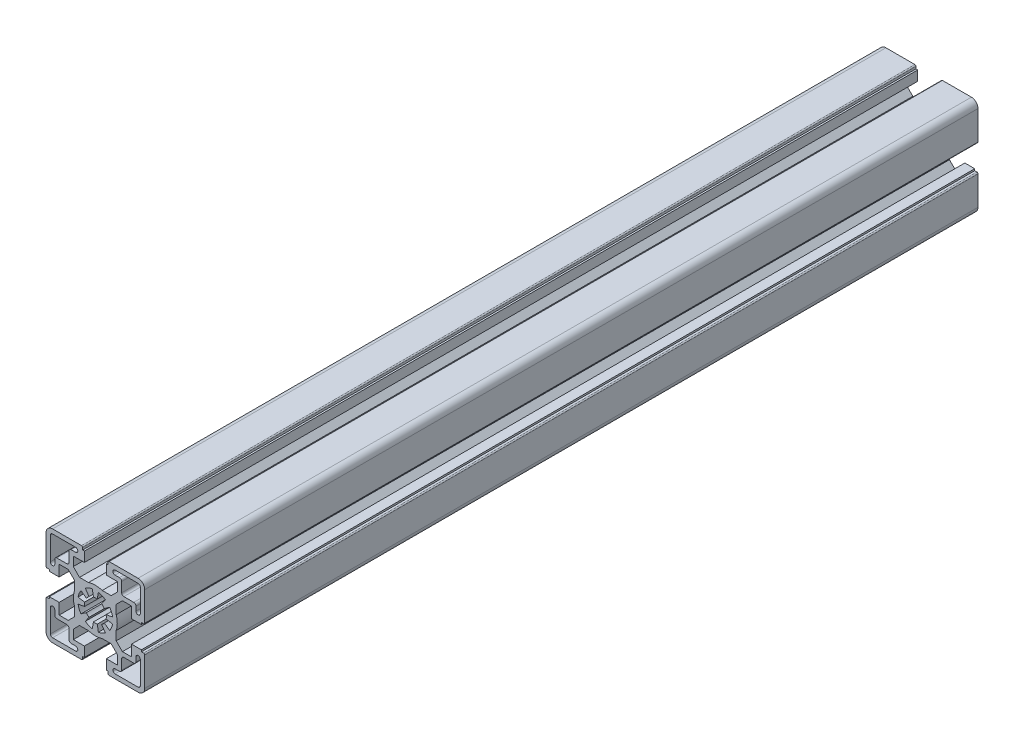
SolidWorks part; units mm, degrees
material "7079 Alloy"
ref_plane "Front Plane" through (0, 0, 0) normal (0, 0, 1) x (1, 0, 0)
ref_plane "Top Plane" through (0, 0, 0) normal (0, 1, 0) x (1, 0, 0)
ref_plane "Right Plane" through (0, 0, 0) normal (1, 0, 0) x (0, 0, -1)
sketch "Sketch1" plane through (0, 0, 0) normal (0, 0, 1) x (1, 0, 0)
  line L0 (0, 34.901) -> (0, -38.8683) construction
  line L1 (-27.7848, 0) -> (42.6814, 0) construction
  line L88 (0.8682, 4.924) -> (1.3892, 7.8784)
  line L89 (-0.8682, 4.924) -> (-1.3892, 7.8785)
  line L90 (-4.5886, 6.5532) -> (-2.8679, 4.0957)
  line L91 (-4.0957, 2.8679) -> (-6.5532, 4.5886)
  line L92 (-7.8784, 1.3892) -> (-4.924, 0.8682)
  line L93 (-7.8785, -1.3892) -> (-4.924, -0.8682)
  line L94 (-6.5532, -4.5886) -> (-4.0957, -2.8679)
  line L95 (-4.5886, -6.5532) -> (-2.8679, -4.0957)
  line L96 (-1.3892, -7.8784) -> (-0.8682, -4.924)
  line L97 (0.8682, -4.924) -> (1.3892, -7.8784)
  line L98 (4.5886, -6.5532) -> (2.8679, -4.0957)
  line L99 (4.0957, -2.8679) -> (6.5532, -4.5886)
  line L100 (7.8784, -1.3892) -> (4.924, -0.8682)
  line L101 (4.924, 0.8682) -> (7.8784, 1.3892)
  line L102 (4.0957, 2.8679) -> (6.5532, 4.5886)
  line L103 (2.8679, 4.0957) -> (4.5886, 6.5532)
  line L104 (-5, -16.4999) -> (-5, -20.9999)
  line L105 (-5, -20.9999) -> (-5.8, -20.9999)
  line L106 (-5.8, -20.9999) -> (-5.8, -22)
  line L107 (-6.3, -22.5) -> (-19.5, -22.5)
  line L108 (-22.5, -19.5) -> (-22.5, -6.2999)
  line L109 (-22, -5.7999) -> (-21, -5.7999)
  line L110 (-21, -5.7999) -> (-21, -4.9999)
  line L111 (-21, -4.9999) -> (-16.5, -4.9999)
  line L112 (-16.5, -4.9999) -> (-16.5, -10.0499)
  line L113 (-16.5, -10.0499) -> (-12.3429, -10.0499)
  line L114 (-12.3429, -10.0499) -> (-9.5, -7.207)
  line L115 (-9.5, -7.207) -> (-9.5, -3.1226)
  line L116 (-9.5, 3.1227) -> (-9.5, 7.207)
  line L117 (-9.5, 7.207) -> (-12.3429, 10.0499)
  line L118 (-12.3429, 10.0499) -> (-16.5, 10.0499)
  line L119 (-16.5, 10.0499) -> (-16.5, 4.9999)
  line L120 (-16.5, 4.9999) -> (-21, 4.9999)
  line L121 (-21, 4.9999) -> (-21, 5.7999)
  line L122 (-21, 5.7999) -> (-22, 5.7999)
  line L123 (-22.5, 6.2999) -> (-22.5, 19.5)
  line L124 (-19.5, 22.5) -> (-6.3, 22.5)
  line L125 (-5.7999, 21.9999) -> (-5.7999, 20.9999)
  line L126 (-5.7999, 20.9999) -> (-5, 20.9999)
  line L127 (-5, 20.9999) -> (-5, 16.5)
  line L128 (-5, 16.5) -> (-10.0501, 16.5)
  line L129 (-10.0501, 16.5) -> (-10.0501, 12.3428)
  line L130 (-10.0501, 12.3428) -> (-7.2072, 9.4999)
  line L131 (-7.2072, 9.4999) -> (-3.1228, 9.4999)
  line L132 (3.1226, 9.4999) -> (7.207, 9.4999)
  line L133 (7.207, 9.4999) -> (10.0499, 12.3428)
  line L134 (10.0499, 12.3428) -> (10.0499, 16.5)
  line L135 (10.0499, 16.5) -> (5, 16.5)
  line L136 (5, 16.5) -> (5, 21)
  line L137 (5, 21) -> (5.7999, 21)
  line L138 (5.7999, 21) -> (5.7999, 21.9999)
  line L139 (6.3, 22.5) -> (19.5001, 22.5)
  line L140 (22.5001, 6.2999) -> (22.5001, 19.5)
  line L141 (22.0001, 5.7999) -> (21, 5.7999)
  line L142 (21, 5.7999) -> (21, 4.9999)
  line L143 (21, 4.9999) -> (16.5, 4.9999)
  line L144 (16.5, 4.9999) -> (16.5, 10.0499)
  line L145 (16.5, 10.0499) -> (12.3429, 10.0499)
  line L146 (12.3429, 10.0499) -> (9.4999, 7.207)
  line L147 (9.4999, 7.207) -> (9.4999, 3.1227)
  line L148 (9.4999, -3.1226) -> (9.4999, -7.207)
  line L149 (9.4999, -7.207) -> (12.3429, -10.0499)
  line L150 (12.3429, -10.0499) -> (16.5, -10.0499)
  line L151 (16.5, -10.0499) -> (16.5, -4.9999)
  line L152 (16.5, -4.9999) -> (21, -4.9999)
  line L153 (21, -4.9999) -> (21, -5.7999)
  line L154 (21, -5.7999) -> (22.0001, -5.7999)
  line L155 (22.5001, -6.2999) -> (22.5001, -19.5)
  line L156 (6.3, -22.5) -> (19.5001, -22.5)
  line L157 (5.8, -22) -> (5.8, -20.9999)
  line L158 (5.8, -20.9999) -> (5, -20.9999)
  line L159 (5, -20.9999) -> (5, -16.4999)
  line L160 (5, -16.4999) -> (10.0499, -16.4999)
  line L161 (10.0499, -16.4999) -> (10.0499, -12.3428)
  line L162 (10.0499, -12.3428) -> (7.2069, -9.4998)
  line L163 (7.2069, -9.4998) -> (3.1226, -9.4998)
  line L164 (-3.1228, -9.4998) -> (-7.2071, -9.4998)
  line L165 (-7.2071, -9.4998) -> (-10.0501, -12.3428)
  line L166 (-10.0501, -12.3428) -> (-10.0501, -16.4999)
  line L167 (-10.0501, -16.4999) -> (-5, -16.4999)
  line L168 (-17.5001, -12) -> (-13.0001, -12)
  line L169 (-12.0001, -17.4999) -> (-12.0001, -13)
  line L170 (-11.0001, -18.4999) -> (-9.0001, -18.4999)
  line L171 (-19.5001, -20.5) -> (-9.0001, -20.5)
  line L172 (-20.5001, -19.5) -> (-20.5001, -8.9999)
  line L173 (-18.5001, -11) -> (-18.5001, -8.9999)
  line L174 (13, -12) -> (17.5, -12)
  line L175 (12, -17.4999) -> (12, -13)
  line L176 (9, -18.4999) -> (11, -18.4999)
  line L177 (9, -20.5) -> (19.5, -20.5)
  line L178 (20.5, -19.5) -> (20.5, -9.0001)
  line L179 (18.5, -11) -> (18.5, -9.0001)
  line L180 (-17.5001, 12) -> (-13.0001, 12)
  line L181 (-12.0001, 13) -> (-12.0001, 17.4999)
  line L182 (-11.0001, 18.4999) -> (-9.0001, 18.4999)
  line L183 (-19.5001, 20.5) -> (-9.0001, 20.5)
  line L184 (-20.5001, 8.9999) -> (-20.5001, 19.5)
  line L185 (-18.5001, 8.9999) -> (-18.5001, 11)
  line L186 (13, 12) -> (17.5, 12)
  line L187 (12, 13) -> (12, 17.4999)
  line L188 (9, 18.4999) -> (11, 18.4999)
  line L189 (9, 20.5) -> (19.5, 20.5)
  line L190 (20.5, 9.0001) -> (20.5, 19.5)
  line L191 (18.5, 9.0001) -> (18.5, 11)
  arc A56 (0.8682, 4.924) -> (-0.8682, 4.924) centre (0, 0) ccw
  arc A57 (-1.3892, 7.8785) -> (-4.5886, 6.5532) centre (0, 0) ccw
  arc A58 (-2.8679, 4.0957) -> (-4.0957, 2.8679) centre (0, 0) ccw
  arc A59 (-6.5532, 4.5886) -> (-7.8784, 1.3892) centre (0, 0) ccw
  arc A60 (-4.924, 0.8682) -> (-4.924, -0.8682) centre (0, 0) ccw
  arc A61 (-7.8785, -1.3892) -> (-6.5532, -4.5886) centre (0, 0) ccw
  arc A62 (-4.0957, -2.8679) -> (-2.8679, -4.0957) centre (0, 0) ccw
  arc A63 (-4.5886, -6.5532) -> (-1.3892, -7.8784) centre (0, 0) ccw
  arc A64 (-0.8682, -4.924) -> (0.8682, -4.924) centre (0, 0) ccw
  arc A65 (1.3892, -7.8784) -> (4.5886, -6.5532) centre (0, 0) ccw
  arc A66 (2.8679, -4.0957) -> (4.0957, -2.8679) centre (0, 0) ccw
  arc A67 (6.5532, -4.5886) -> (7.8784, -1.3892) centre (0, 0) ccw
  arc A68 (4.924, -0.8682) -> (4.924, 0.8682) centre (0, 0) ccw
  arc A69 (7.8784, 1.3892) -> (6.5532, 4.5886) centre (0, 0) ccw
  arc A70 (4.0957, 2.8679) -> (2.8679, 4.0957) centre (0, 0) ccw
  arc A71 (4.5886, 6.5532) -> (1.3892, 7.8784) centre (0, 0) ccw
  arc A72 (-6.3, -22.5) -> (-5.8, -22) centre (-6.3, -22) ccw
  arc A73 (-22.5, -19.5) -> (-19.5, -22.5) centre (-19.5, -19.5) ccw
  arc A74 (-22, -5.7999) -> (-22.5, -6.2999) centre (-22, -6.2999) ccw
  arc A75 (-9.5, 3.1227) -> (-9.5, -3.1226) centre (0, 0.0001) ccw
  arc A76 (-22.5, 6.2999) -> (-22, 5.7999) centre (-22, 6.2999) ccw
  arc A77 (-19.5, 22.5) -> (-22.5, 19.5) centre (-19.5, 19.5) ccw
  arc A78 (-5.7999, 21.9999) -> (-6.3, 22.5) centre (-6.3, 21.9999) ccw
  arc A79 (3.1226, 9.4999) -> (-3.1228, 9.4999) centre (-0.0001, -0.0001) ccw
  arc A80 (6.3, 22.5) -> (5.7999, 21.9999) centre (6.3, 21.9999) ccw
  arc A81 (22.5001, 19.5) -> (19.5001, 22.5) centre (19.5001, 19.5) ccw
  arc A82 (22.0001, 5.7999) -> (22.5001, 6.2999) centre (22.0001, 6.2999) ccw
  arc A83 (9.4999, -3.1226) -> (9.4999, 3.1227) centre (0, 0.0001) ccw
  arc A84 (22.5001, -6.2999) -> (22.0001, -5.7999) centre (22.0001, -6.2999) ccw
  arc A85 (19.5001, -22.5) -> (22.5001, -19.5) centre (19.5001, -19.5) ccw
  arc A86 (5.8, -22) -> (6.3, -22.5) centre (6.3, -22) ccw
  arc A87 (-3.1228, -9.4998) -> (3.1226, -9.4998) centre (-0.0001, 0.0001) ccw
  arc A88 (-18.5001, -11) -> (-17.5001, -12) centre (-17.5001, -11) ccw
  arc A89 (-12.0001, -13) -> (-13.0001, -12) centre (-13.0001, -13) ccw
  arc A90 (-12.0001, -17.4999) -> (-11.0001, -18.4999) centre (-11.0001, -17.4999) ccw
  arc A91 (-9.0001, -20.5) -> (-9.0001, -18.4999) centre (-9.0001, -19.5) ccw
  arc A92 (-20.5001, -19.5) -> (-19.5001, -20.5) centre (-19.5001, -19.5) ccw
  arc A93 (-18.5001, -8.9999) -> (-20.5001, -8.9999) centre (-19.5001, -8.9999) ccw
  arc A94 (17.5, -12) -> (18.5, -11) centre (17.5, -11) ccw
  arc A95 (13, -12) -> (12, -13) centre (13, -13) ccw
  arc A96 (11, -18.4999) -> (12, -17.4999) centre (11, -17.4999) ccw
  arc A97 (9, -18.4999) -> (9, -20.5) centre (9, -19.5) ccw
  arc A98 (19.5, -20.5) -> (20.5, -19.5) centre (19.5, -19.5) ccw
  arc A99 (20.5, -9.0001) -> (18.5, -9.0001) centre (19.5, -9.0001) ccw
  arc A100 (-17.5001, 12) -> (-18.5001, 11) centre (-17.5001, 11) ccw
  arc A101 (-13.0001, 12) -> (-12.0001, 13) centre (-13.0001, 13) ccw
  arc A102 (-11.0001, 18.4999) -> (-12.0001, 17.4999) centre (-11.0001, 17.4999) ccw
  arc A103 (-9.0001, 18.4999) -> (-9.0001, 20.5) centre (-9.0001, 19.5) ccw
  arc A104 (-19.5001, 20.5) -> (-20.5001, 19.5) centre (-19.5001, 19.5) ccw
  arc A105 (-20.5001, 8.9999) -> (-18.5001, 8.9999) centre (-19.5001, 8.9999) ccw
  arc A106 (18.5, 11) -> (17.5, 12) centre (17.5, 11) ccw
  arc A107 (12, 13) -> (13, 12) centre (13, 13) ccw
  arc A108 (12, 17.4999) -> (11, 18.4999) centre (11, 17.4999) ccw
  arc A109 (9, 20.5) -> (9, 18.4999) centre (9, 19.5) ccw
  arc A110 (20.5, 19.5) -> (19.5, 20.5) centre (19.5, 19.5) ccw
  arc A111 (18.5, 9.0001) -> (20.5, 9.0001) centre (19.5, 9.0001) ccw
  dimension "D5" = 10
  dimension "D1" = 45.0001
  dimension "D2" = 44.9999
  dimension "D3" = 12.5001
  dimension "D4" = 10
  dimension "D6" = 22.5001
extrude "Base-Extrude" add sketch "Sketch1" along normal blind 380
